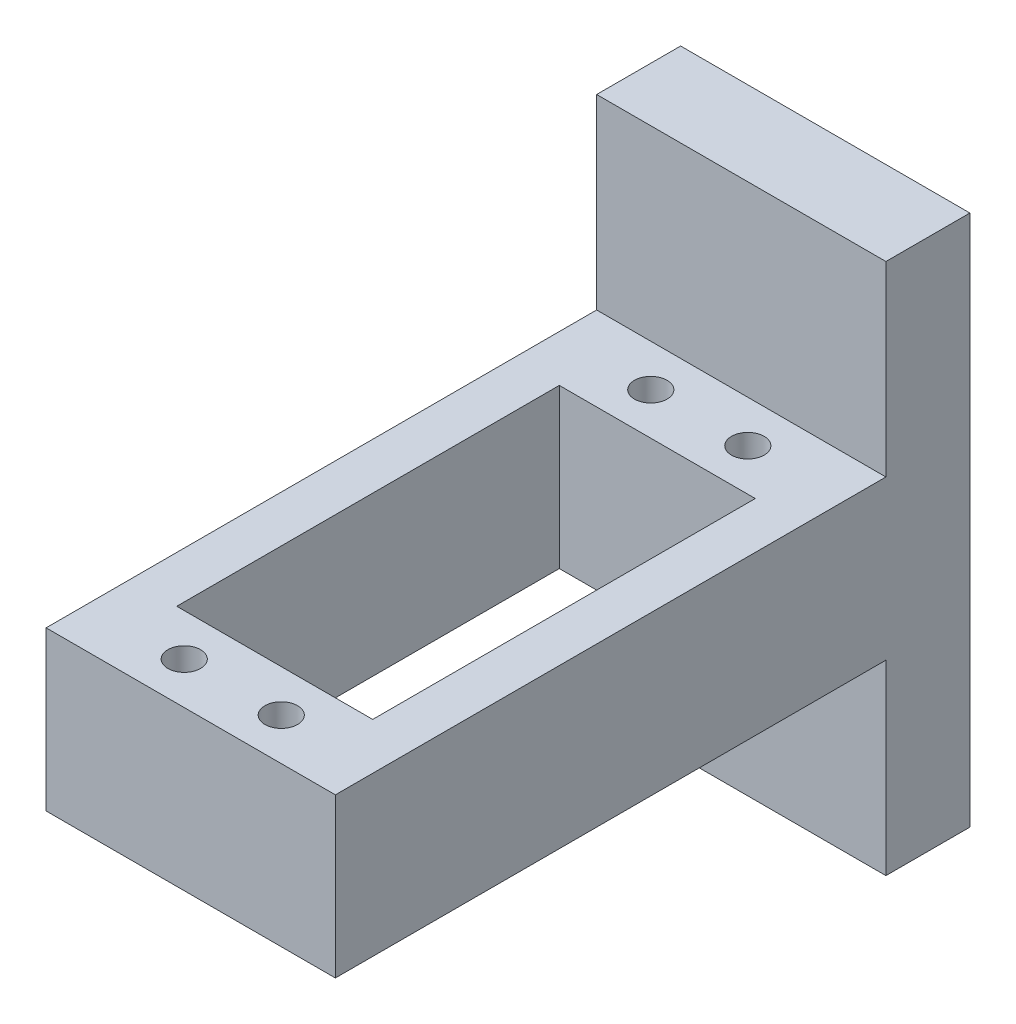
SolidWorks part; units mm, degrees
ref_plane "Front Plane" through (0, 0, 0) normal (0, 0, 1) x (1, 0, 0)
ref_plane "Top Plane" through (0, 0, 0) normal (0, 1, 0) x (1, 0, 0)
ref_plane "Right Plane" through (0, 0, 0) normal (1, 0, 0) x (0, 0, -1)
sketch "Sketch1" plane through (0, 0, 0) normal (0, 0, 1) x (1, 0, 0)
  line L0 (-15.5, -28.5) -> (-8.5, -28.5) construction
  line L1 (15.5, -28.5) -> (-15.5, -28.5)
  line L2 (15.5, -28.5) -> (15.5, 28.5)
  line L3 (15.5, 28.5) -> (-15.5, 28.5)
  line L4 (-15.5, -28.5) -> (-15.5, -10.3)
  line L5 (15.5, -28.5) -> (-15.5, 28.5) construction
  line L6 (-15.5, 10.3) -> (-15.5, -10.3)
  line L8 (-15.5, -28.5) -> (-15.5, -10.3) construction
  line L13 (-15.5, 10.3) -> (-15.5, 28.5)
  point P0 (0, 0)
  dimension "D1" = 31
  dimension "D2" = 57
  dimension "D3" = 7
  dimension "D4" = 15.5
  dimension "D7" = 18.2
extrude "Boss-Extrude1" add sketch "Sketch1" along normal blind 9
sketch "Sketch10" plane through (0, 0, 9) normal (0, 0, 1) x (1, 0, 0)
  line L0 (-15.5, 28.5) -> (-15.5, -28.5) construction
  line L1 (15.5, -8.5) -> (-15.5, -8.5)
  line L2 (15.5, -8.5) -> (15.5, 8.5)
  line L3 (15.5, 8.5) -> (-15.5, 8.5)
  line L4 (-15.5, -8.5) -> (-15.5, 8.5)
  line L5 (15.5, -8.5) -> (-15.5, 8.5) construction
  line L6 (15.5, 8.5) -> (-15.5, -8.5) construction
  point P0 (0, 0)
  dimension "D1" = 17
extrude "Boss-Extrude5" add sketch "Sketch10" along normal blind 59
sketch "Sketch11" plane through (0, -8.5, 0) normal (0, -1, 0) x (1, 0, 0)
  line L0 (0, 0) -> (0, 9) construction
  line L1 (-15.5, 9) -> (15.5, 9) construction
  line L2 (0, 9) -> (0, 18) construction
  line L3 (-10.5, 18) -> (-10.5, 59)
  line L4 (-10.5, 18) -> (10.5, 18)
  line L5 (0, 13.5) -> (5.2, 13.5) construction
  line L6 (-10.5, 59) -> (10.5, 59)
  line L7 (10.5, 18) -> (10.5, 59)
  line L8 (-10.5, 38.5) -> (10.5, 38.5) construction
  circle A0 centre (5.2, 13.5) radius 1.75
  circle A1 centre (-5.2, 13.5) radius 1.75
  circle A2 centre (5.2, 63.5) radius 1.75
  circle A3 centre (-5.2, 63.5) radius 1.75
  dimension "D6" = 3.5
  dimension "D1" = 9
  dimension "D2" = 41
  dimension "D3" = 10.5
  dimension "D4" = 41
  dimension "D5" = 5.2
extrude "Cut-Extrude6" cut sketch "Sketch11" against normal through all
sketch "Sketch12" plane through (0, 0, 0) normal (0, 0, -1) x (-1, 0, 0)
  line L0 (0, 0) -> (15.5, 0) construction
  line L1 (15.5, 28.5) -> (15.5, -28.5) construction
  line L2 (15.5, 0) -> (11.5, 0) construction
  line L3 (11.5, 0) -> (11.5, 25) construction
  line L4 (0, 0) -> (0, 28.5) construction
  line L5 (-15.5, 28.5) -> (15.5, 28.5) construction
  circle A0 centre (11.5, 25) radius 1.75
  circle A1 centre (-11.5, 25) radius 1.75
  circle A2 centre (11.5, -25) radius 1.75
  circle A3 centre (-11.5, -25) radius 1.75
  dimension "D3" = 3.5
  dimension "D1" = 4
  dimension "D2" = 25
extrude "Cut-Extrude7" cut sketch "Sketch12" against normal blind 3
